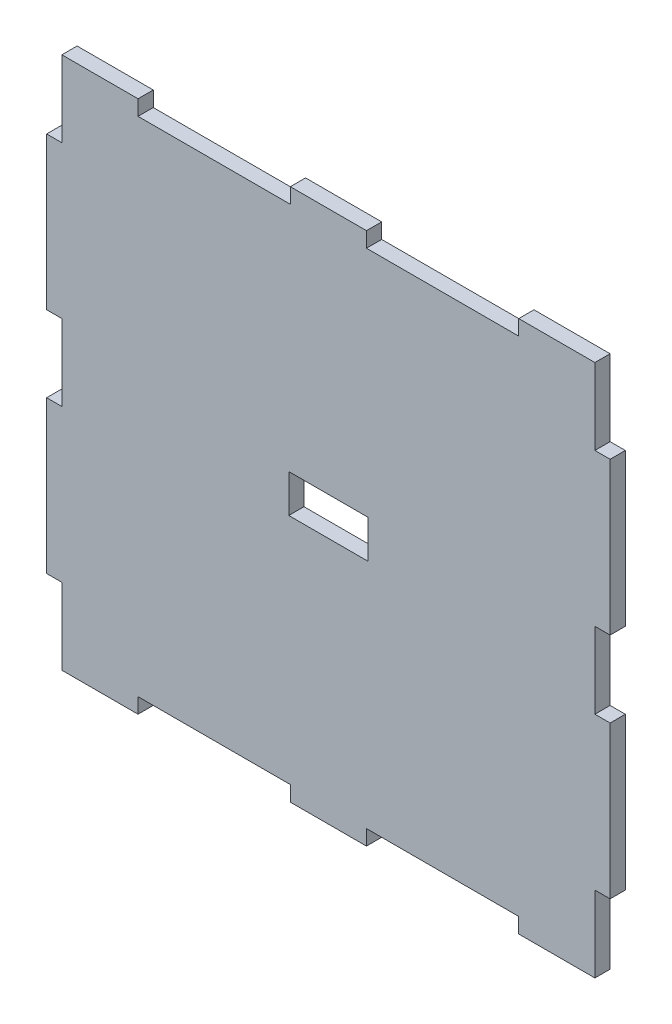
SolidWorks part; units mm, degrees
ref_plane "Front Plane" through (0, 0, 0) normal (0, 0, 1) x (1, 0, 0)
ref_plane "Top Plane" through (0, 0, 0) normal (0, 1, 0) x (1, 0, 0)
ref_plane "Right Plane" through (0, 0, 0) normal (1, 0, 0) x (0, 0, -1)
sketch "Sketch1" plane through (0, 0, 0) normal (0, 0, 1) x (1, 0, 0)
  line L1 (-35, -35) -> (35, -35)
  line L2 (-35, -35) -> (-35, 35)
  line L3 (-35, 35) -> (35, 35)
  line L4 (35, -35) -> (35, 35)
  line L5 (0, 35) -> (0, -35) construction
  line L6 (-35, 0) -> (35, 0) construction
  line L11 (0, 18) -> (0, -18) construction
  line L12 (-17.25, 0) -> (17.25, 0) construction
  point P0 (0, 0)
  point P4 (0, 0)
  dimension "D1" = 70
  dimension "D2" = 70
extrude "Boss-Extrude1" add sketch "Sketch1" against normal blind 2
sketch "Sketch2" plane through (0, 0, 0) normal (0, 0, 1) x (1, 0, 0)
  line L0 (-35, 35) -> (-25, 35)
  line L1 (35, 35) -> (-35, 35) construction
  line L2 (-25, 35) -> (-5, 35)
  line L3 (-5, 35) -> (5, 35)
  line L4 (5, 35) -> (25, 35)
  line L6 (35, 35) -> (35, 25)
  line L7 (-25, 33) -> (-5, 33)
  line L8 (-25, 33) -> (-25, 37)
  line L9 (-25, 37) -> (-5, 37)
  line L10 (-5, 33) -> (-5, 37)
  line L11 (-15, 37) -> (-15, 33) construction
  line L12 (-25, 35) -> (-5, 35) construction
  line L13 (5, 33) -> (25, 33)
  line L14 (5, 33) -> (5, 37)
  line L15 (5, 37) -> (25, 37)
  line L16 (25, 33) -> (25, 37)
  line L17 (15, 37) -> (15, 33) construction
  line L18 (5, 35) -> (25, 35) construction
  line L19 (35, -35) -> (35, 35) construction
  line L20 (35, 25) -> (35, 5)
  line L21 (35, 5) -> (35, -5)
  line L22 (35, -5) -> (35, -25)
  line L23 (-35, -35) -> (-25, -35)
  line L24 (35, -5) -> (33, -5)
  line L25 (35, -5) -> (35, -25)
  line L26 (35, -25) -> (33, -25)
  line L27 (33, -5) -> (33, -25)
  line L28 (35, 25) -> (33, 25)
  line L29 (35, 25) -> (35, 5)
  line L30 (35, 5) -> (33, 5)
  line L31 (33, 25) -> (33, 5)
  line L32 (-35, -35) -> (35, -35) construction
  line L33 (-25, -35) -> (-5, -35)
  line L34 (-5, -35) -> (5, -35)
  line L35 (5, -35) -> (25, -35)
  line L36 (-35, 35) -> (-35, 25)
  line L37 (-25, -35) -> (-5, -35)
  line L38 (-25, -35) -> (-25, -33)
  line L39 (-25, -33) -> (-5, -33)
  line L40 (-5, -35) -> (-5, -33)
  line L41 (5, -35) -> (25, -35)
  line L42 (5, -35) -> (5, -33)
  line L43 (5, -33) -> (25, -33)
  line L44 (25, -35) -> (25, -33)
  line L45 (-35, 35) -> (-35, -35) construction
  line L46 (-35, 25) -> (-35, 5)
  line L47 (-35, 5) -> (-35, -5)
  line L48 (-35, -5) -> (-35, -25)
  line L49 (-35, 25) -> (-37, 25)
  line L50 (-35, 25) -> (-33, 25)
  line L51 (-35, 25) -> (-35, 5)
  line L52 (-35, 5) -> (-33, 5)
  line L53 (-33, 25) -> (-33, 5)
  line L54 (-35, -5) -> (-33, -5)
  line L55 (-35, -5) -> (-35, -25)
  line L56 (-35, -25) -> (-33, -25)
  line L57 (-33, -5) -> (-33, -25)
  line L58 (-35, 25) -> (-35, 5)
  line L59 (-35, 5) -> (-37, 5)
  line L60 (-37, 25) -> (-37, 5)
  line L61 (-35, -5) -> (-37, -5)
  line L62 (-35, -5) -> (-35, -25)
  line L63 (-35, -25) -> (-37, -25)
  line L64 (-37, -5) -> (-37, -25)
  line L65 (-25, -35) -> (-5, -35)
  line L66 (-25, -35) -> (-25, -37)
  line L67 (-25, -37) -> (-5, -37)
  line L68 (-5, -35) -> (-5, -37)
  line L69 (5, -35) -> (25, -35)
  line L70 (5, -35) -> (5, -37)
  line L71 (5, -37) -> (25, -37)
  line L72 (25, -35) -> (25, -37)
  line L73 (35, -25) -> (37, -25)
  line L74 (35, -25) -> (35, -5)
  line L75 (35, -5) -> (37, -5)
  line L76 (37, -25) -> (37, -5)
  line L77 (35, 5) -> (37, 5)
  line L78 (35, 5) -> (35, 25)
  line L79 (35, 25) -> (37, 25)
  line L80 (37, 5) -> (37, 25)
  point P7 (15, 35)
  point P9 (-15, 35)
  point P10 (-15, 35)
  point P14 (15, 35)
  line M25 (35, -35) -> (35, 35)
  line M27 (-35, 35) -> (-35, -35)
  dimension "D1" = 10
  dimension "D2" = 20
  dimension "D3" = 10
  dimension "D4" = 20
  dimension "D5" = 4
  dimension "D6" = 20
  dimension "D7" = 20
  dimension "D8" = 4
  dimension "D9" = 10
  dimension "D10" = 20
  dimension "D11" = 10
  dimension "D12" = 20
  dimension "D13" = 2
  dimension "D14" = 2
  dimension "D15" = 10
  dimension "D16" = 20
  dimension "D17" = 10
  dimension "D18" = 20
  dimension "D19" = 20
  dimension "D20" = 20
  dimension "D21" = 2
  dimension "D22" = 2
  dimension "D23" = 10
  dimension "D24" = 20
  dimension "D25" = 10
  dimension "D26" = 20
  dimension "D27" = 2
  dimension "D28" = 2
  dimension "D29" = 2
  dimension "D30" = 2
  dimension "D31" = 2
  dimension "D32" = 2
  dimension "D33" = 2
  dimension "D34" = 2
sketch "Sketch3" plane through (0, 0, 0) normal (0, 0, 1) x (1, 0, 0)
  line L0 (-35, 35) -> (-25, 35)
  line L2 (-25, 35) -> (-5, 35)
  line L3 (-5, 35) -> (5, 35)
  line L4 (5, 35) -> (25, 35)
  line L6 (35, 35) -> (35, 25)
  line L7 (-25, 33) -> (-5, 33)
  line L8 (-25, 33) -> (-25, 37)
  line L9 (-25, 37) -> (-5, 37)
  line L10 (-5, 33) -> (-5, 37)
  line L11 (-15, 37) -> (-15, 33) construction
  line L12 (-25, 35) -> (-5, 35) construction
  line L13 (5, 33) -> (25, 33)
  line L14 (5, 33) -> (5, 37)
  line L15 (5, 37) -> (25, 37)
  line L16 (25, 33) -> (25, 37)
  line L17 (15, 37) -> (15, 33) construction
  line L18 (5, 35) -> (25, 35) construction
  line L20 (35, 25) -> (35, 5)
  line L21 (35, 5) -> (35, -5)
  line L22 (35, -5) -> (35, -25)
  line L23 (-35, -35) -> (-25, -35)
  line L24 (35, -5) -> (33, -5)
  line L25 (35, -5) -> (35, -25)
  line L26 (35, -25) -> (33, -25)
  line L27 (33, -5) -> (33, -25)
  line L28 (35, 25) -> (33, 25)
  line L29 (35, 25) -> (35, 5)
  line L30 (35, 5) -> (33, 5)
  line L31 (33, 25) -> (33, 5)
  line L33 (-25, -35) -> (-5, -35)
  line L34 (-5, -35) -> (5, -35)
  line L35 (5, -35) -> (25, -35)
  line L36 (-35, 35) -> (-35, 25)
  line L37 (-25, -35) -> (-5, -35)
  line L38 (-25, -35) -> (-25, -33)
  line L39 (-25, -33) -> (-5, -33)
  line L40 (-5, -35) -> (-5, -33)
  line L41 (5, -35) -> (25, -35)
  line L42 (5, -35) -> (5, -33)
  line L43 (5, -33) -> (25, -33)
  line L44 (25, -35) -> (25, -33)
  line L46 (-35, 25) -> (-35, 5)
  line L47 (-35, 5) -> (-35, -5)
  line L48 (-35, -5) -> (-35, -25)
  line L49 (-35, 25) -> (-37, 25)
  line L50 (-35, 25) -> (-33, 25)
  line L51 (-35, 25) -> (-35, 5)
  line L52 (-35, 5) -> (-33, 5)
  line L53 (-33, 25) -> (-33, 5)
  line L54 (-35, -5) -> (-33, -5)
  line L55 (-35, -5) -> (-35, -25)
  line L56 (-35, -25) -> (-33, -25)
  line L57 (-33, -5) -> (-33, -25)
  line L58 (-35, 25) -> (-35, 5)
  line L59 (-35, 5) -> (-37, 5)
  line L60 (-37, 25) -> (-37, 5)
  line L61 (-35, -5) -> (-37, -5)
  line L62 (-35, -5) -> (-35, -25)
  line L63 (-35, -25) -> (-37, -25)
  line L64 (-37, -5) -> (-37, -25)
  line L65 (-25, -35) -> (-5, -35)
  line L66 (-25, -35) -> (-25, -37)
  line L67 (-25, -37) -> (-5, -37)
  line L68 (-5, -35) -> (-5, -37)
  line L69 (5, -35) -> (25, -35)
  line L70 (5, -35) -> (5, -37)
  line L71 (5, -37) -> (25, -37)
  line L72 (25, -35) -> (25, -37)
  line L73 (35, -25) -> (37, -25)
  line L74 (35, -25) -> (35, -5)
  line L75 (35, -5) -> (37, -5)
  line L76 (37, -25) -> (37, -5)
  line L77 (35, 5) -> (37, 5)
  line L78 (35, 5) -> (35, 25)
  line L79 (35, 25) -> (37, 25)
  line L80 (37, 5) -> (37, 25)
  point P7 (15, 35)
  point P9 (-15, 35)
  point P10 (-15, 35)
  point P14 (15, 35)
  dimension "D1" = 10
  dimension "D2" = 20
  dimension "D3" = 10
  dimension "D4" = 20
  dimension "D5" = 4
  dimension "D6" = 20
  dimension "D7" = 20
  dimension "D8" = 4
  dimension "D9" = 10
  dimension "D10" = 20
  dimension "D11" = 10
  dimension "D12" = 20
  dimension "D13" = 2
  dimension "D14" = 2
  dimension "D15" = 10
  dimension "D16" = 20
  dimension "D17" = 10
  dimension "D18" = 20
  dimension "D19" = 20
  dimension "D20" = 20
  dimension "D21" = 2
  dimension "D22" = 2
  dimension "D23" = 10
  dimension "D24" = 20
  dimension "D25" = 10
  dimension "D26" = 20
  dimension "D27" = 2
  dimension "D28" = 2
  dimension "D29" = 2
  dimension "D30" = 2
  dimension "D31" = 2
  dimension "D32" = 2
  dimension "D33" = 2
  dimension "D34" = 2
extrude "Boss-Extrude2" add sketch "Sketch2" against normal blind 2 contours L49 L60 L59 M27 | L61 L64 L63 M27 | L73 L76 L75 M25 | L77 L80 L79 M25
extrude "Cut-Extrude1" cut sketch "Sketch3" against normal blind 2 contours L7 L10 L2 L8 | L13 L16 L4 L14 | L33 L40 L39 L38 | L35 L44 L43 L42
sketch "Sketch4" plane through (0, 0, 0) normal (0, 0, 1) x (1, 0, 0)
  line L1 (-5.205, -2.5) -> (5.205, -2.5)
  line L2 (-5.205, -2.5) -> (-5.205, 2.5)
  line L3 (-5.205, 2.5) -> (5.205, 2.5)
  line L4 (5.205, -2.5) -> (5.205, 2.5)
  line L5 (0, 2.5) -> (0, -2.5) construction
  line L6 (-5.205, 0) -> (5.205, 0) construction
  point P0 (0, 0)
  dimension "D1" = 10.41
  dimension "D2" = 5
extrude "Cut-Extrude2" cut sketch "Sketch4" against normal blind 10
